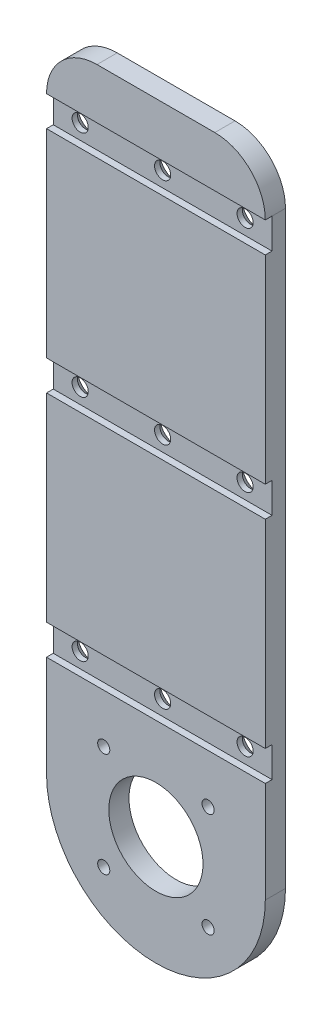
SolidWorks part; units mm, degrees
ref_plane "Front Plane" through (0, 0, 0) normal (0, 0, 1) x (1, 0, 0)
ref_plane "Top Plane" through (0, 0, 0) normal (0, 1, 0) x (1, 0, 0)
ref_plane "Right Plane" through (0, 0, 0) normal (1, 0, 0) x (0, 0, -1)
sketch "Sketch1" plane through (0, 0, 0) normal (0, 0, 1) x (1, 0, 0)
  line L1 (-32.5, -95) -> (32.5, -95)
  line L2 (-32.5, -95) -> (-32.5, 95)
  line L3 (-32.5, 95) -> (32.5, 95)
  line L4 (32.5, -95) -> (32.5, 95)
  line L5 (-32.5, -95) -> (32.5, 95) construction
  line L6 (-32.5, 95) -> (32.5, -95) construction
  line L7 (15.5, -110.5) -> (-15.5, -110.5)
  line L8 (15.5, -110.5) -> (15.5, -79.5)
  line L9 (15.5, -79.5) -> (-15.5, -79.5)
  line L10 (-15.5, -110.5) -> (-15.5, -79.5)
  line L11 (15.5, -110.5) -> (-15.5, -79.5) construction
  line L12 (15.5, -79.5) -> (-15.5, -110.5) construction
  circle A0 centre (0, -95) radius 32.5
  circle A1 centre (0, -95) radius 42 construction
  circle A2 centre (0, -95) radius 14
  point P0 (0, 0)
  point P14 (0, -127.5)
  dimension "D1" = 84
  dimension "D4" = 28
  dimension "D2" = 31
  dimension "D3" = 31
  dimension "D5" = 65
  dimension "D6" = 190
  dimension "D7" = 222.5
extrude "Boss-Extrude1" add sketch "Sketch1" along normal blind 6 contours A0 L4 L3 L2 | L1 A0 L10 L9 L8 | L1 A0 L8 L7 L10 | A2 L1 L10 L7 L8 | A2 L1 L8 L9 L10
hole_wizard "M3 Clearance Hole1" positions "Sketch2" profile "Sketch3" hole size "M3" standard "ANSI Metric"
sketch "Sketch2" plane through (0, 0, 0) normal (0, 0, -1) x (-1, 0, 0)
  point P0 (-15.5, -110.5)
  point P3 (15.5, -110.5)
  point P6 (15.5, -79.5)
  point P9 (-15.5, -79.5)
sketch "Sketch3" plane through (15.5, -110.5, 0) normal (1, 0, 0) x (0, 1, 0)
  line L0 (0, 0) -> (0, 7.0815)
  line L1 (0, 7.0815) -> (1.8, 6)
  line L2 (1.8, 6) -> (1.8, 0)
  line L5 (1.8, 0) -> (0, 0)
  line L10 (0, 7.0815) -> (-1.8, 6) construction
  line L11 (0, -6.35) -> (0, 107.95) construction
  dimension "Hole Dia." = 3.6
  dimension "Hole Depth" = 6
  dimension "Drill Angle" = 118
fillet "Fillet1" radius 15 2 edges at (-32.5, 95, 3) (32.5, 95, 3)
sketch "Sketch4" plane through (0, 0, 6) normal (0, 0, 1) x (1, 0, 0)
  line L0 (32.5, -95) -> (32.5, 80) construction
  line L1 (32.5, -65) -> (-32.5, -65)
  line L2 (32.5, -65) -> (32.5, -56)
  line L3 (32.5, -56) -> (-32.5, -56)
  line L4 (-32.5, -65) -> (-32.5, -56)
  line L5 (-32.5, -95) -> (-32.5, 80) construction
  line L6 (0, 12) -> (0, 3)
  line L7 (32.5, 80) -> (-32.5, 80)
  line L8 (32.5, 80) -> (32.5, 71)
  line L9 (32.5, 71) -> (-32.5, 71)
  line L10 (-32.5, 80) -> (-32.5, 71)
  line L11 (-32.5, 12) -> (32.5, 12)
  line L12 (-32.5, 12) -> (-32.5, 3)
  line L13 (-32.5, 3) -> (32.5, 3)
  line L14 (32.5, 12) -> (32.5, 3)
  point P20 (0, 7.5)
  line M15 (-32.5, 80) -> (-32.5, -95)
  line M17 (32.5, -95) -> (32.5, 80)
  dimension "D1" = 9
  dimension "D2" = 9
  dimension "D3" = 9
  dimension "D4" = 30
  dimension "D5" = 127
  dimension "D6" = 63.5
extrude "Cut-Extrude1" cut sketch "Sketch4" against normal blind 2 contours L9 L7 M17 M15 | L13 L6 L11 M15 | L6 L13 L11 M17 | L3 L1 M17 M15
hole_wizard "M4 Clearance Hole1" positions "Sketch5" profile "Sketch6" hole size "M4" standard "ANSI Metric"
sketch "Sketch5" plane through (0, 0, 4) normal (0, 0, 1) x (1, 0, 0)
  line L0 (-32.5, 75.5) -> (32.5, 75.5)
  line L1 (-32.5, 80) -> (-32.5, 71) construction
  line L2 (32.5, 71) -> (32.5, 80) construction
  line L4 (-32.5, 7.5) -> (32.5, 7.5)
  line L5 (-32.5, 12) -> (-32.5, 3) construction
  line L6 (32.5, 3) -> (32.5, 12) construction
  line L8 (-32.5, -60.5) -> (32.5, -60.5)
  line L9 (-32.5, -56) -> (-32.5, -65) construction
  line L10 (32.5, -65) -> (32.5, -56) construction
  point P24 (-24.5, 75.5)
  point P26 (24.5, 75.5)
  point P28 (0, 75.5)
  point P30 (-24.5, 7.5)
  point P32 (0, 7.5)
  point P34 (24.5, 7.5)
  point P36 (24.5, -60.5)
  point P38 (0, -60.5)
  point P40 (-24.5, -60.5)
  dimension "D1" = 8
  dimension "D2" = 8
sketch "Sketch6" plane through (-24.5, -60.5, 4) normal (1, 0, 0) x (0, -1, 0)
  line L0 (0, 0) -> (0, 7.4421)
  line L1 (0, 7.4421) -> (2.4, 6)
  line L2 (2.4, 6) -> (2.4, 0)
  line L5 (2.4, 0) -> (0, 0)
  line L10 (0, 7.4421) -> (-2.4, 6) construction
  line L11 (0, -6.35) -> (0, 107.95) construction
  dimension "Hole Dia." = 4.8
  dimension "Hole Depth" = 6
  dimension "Drill Angle" = 118
chamfer "Chamfer1" distance 2.4 13 edges at (13.7, -110.5, 0) (-17.3, -110.5, 0) (-17.3, -79.5, 0) (13.7, -79.5, 0) (-22.1, 75.5, 0) (2.4, 75.5, 0) (26.9, 75.5, 0) (26.9, 7.5, 0) (2.4, 7.5, 0) (-22.1, 7.5, 0) (-22.1, -60.5, 0) (2.4, -60.5, 0) (26.9, -60.5, 0)
